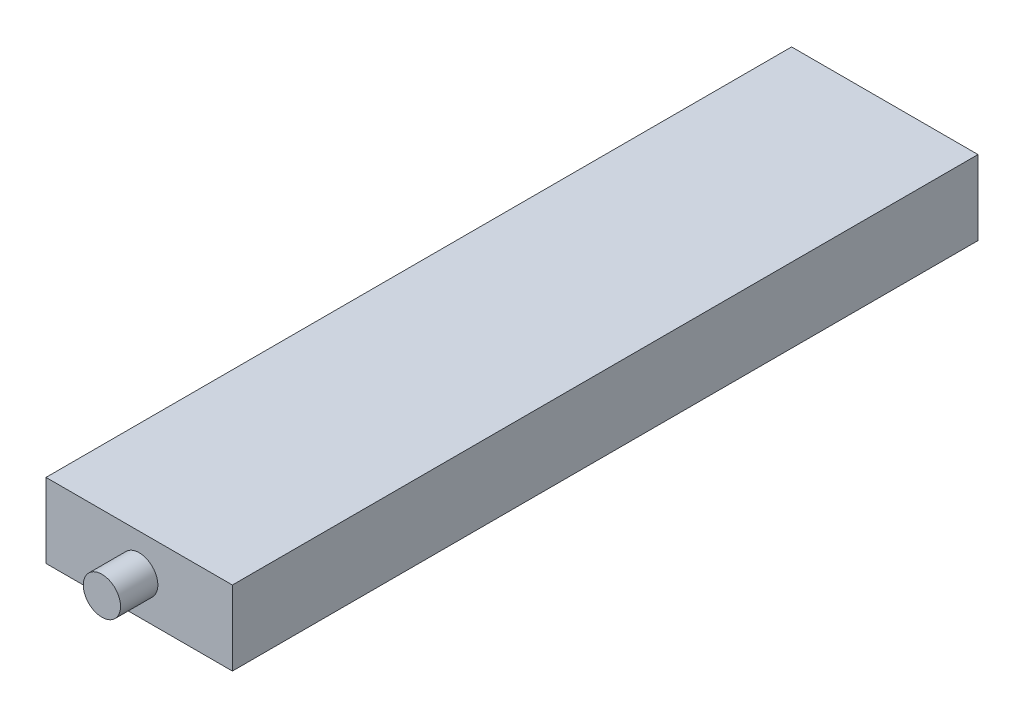
SolidWorks part; units mm, degrees
ref_plane "前视基准面" through (0, 0, 0) normal (0, 0, 1) x (1, 0, 0)
ref_plane "上视基准面" through (0, 0, 0) normal (0, 1, 0) x (1, 0, 0)
ref_plane "右视基准面" through (0, 0, 0) normal (1, 0, 0) x (0, 0, -1)
other "Configuration Table"
sketch "草图1" plane through (0, 0, 0) normal (0, 1, 0) x (1, 0, 0)
  line L0 (0, 0) -> (0, -200)
  line L1 (0, -200) -> (50, -200)
  line L2 (50, -200) -> (50, 0)
  line L3 (50, 0) -> (0, 0)
  dimension "D1" = 200
  dimension "D2" = 50
extrude "凸台-拉伸1" add sketch "草图1" along normal mid plane 20
sketch "草图2" plane through (0, 0, 200) normal (0, 0, 1) x (1, 0, 0)
  line L0 (25, 10) -> (25, -10) construction
  line L1 (0, 10) -> (50, 10) construction
  line L2 (0, -10) -> (50, -10) construction
  circle A0 centre (25, 0) radius 5
extrude "凸台-拉伸2" add sketch "草图2" along normal mid plane 20
